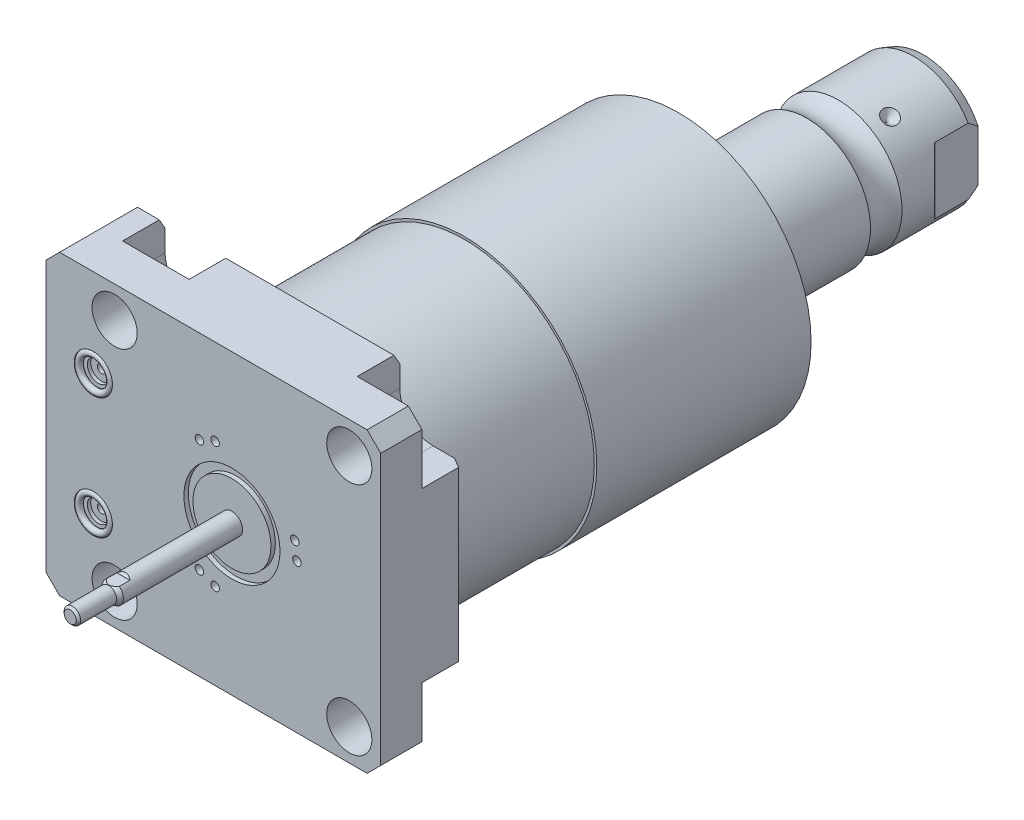
SolidWorks part; units mm, degrees
material "Alloy Steel"
ref_plane "Front Plane" through (0, 0, 0) normal (0, 0, 1) x (1, 0, 0)
ref_plane "Top Plane" through (0, 0, 0) normal (0, 1, 0) x (1, 0, 0)
ref_plane "Right Plane" through (0, 0, 0) normal (1, 0, 0) x (0, 0, -1)
sketch "Sketch1" plane through (0, 0, 0) normal (0, 0, 1) x (1, 0, 0)
  line L0 (-55.55, 44.45) -> (44.45, 44.45)
  line L1 (44.45, 44.45) -> (44.45, -44.45)
  line L2 (44.45, -44.45) -> (-55.55, -44.45)
  line L3 (-55.55, -44.45) -> (-55.55, 44.45)
  dimension "D1" = 100
  dimension "D2" = 88.9
  dimension "D3" = 44.45
  dimension "D4" = 44.45
extrude "Extrude1" add sketch "Sketch1" along normal blind 25.019
hole_wizard "Hole1" positions "Sketch22" profile "Sketch21" legacy end condition through all
sketch "Sketch22" plane through (0, 0, 0) normal (0, 0, -1) x (-1, 0, 0)
  line L0 (0, 0) -> (42.7441, 0) construction
  line L1 (0, 0.8532) -> (0, 27.5062) construction
  point P0 (-35.052, -35.052)
  point P9 (-35.052, 35.052)
  point P11 (35.052, 35.052)
  point P12 (35.052, -35.052)
  dimension "D1" = 35.052
  dimension "D2" = 35.052
sketch "Sketch21" plane through (35.052, -35.052, 0) normal (1, 0, 0) x (0, 1, 0)
  line L0 (0, 0) -> (0, 25.019)
  line L1 (0, 25.019) -> (6.7435, 25.019)
  line L2 (6.7435, 25.019) -> (6.7435, 0)
  line L3 (6.7435, 0) -> (0, 0)
  line L4 (0, 110) -> (0, -10) construction
  dimension "Diameter" = 13.487
  dimension "Depth" = 25.019
sketch "Sketch3" plane through (0, 0, 0) normal (0, 0, -1) x (-1, 0, 0)
  line L0 (-35.052, -25.1205) -> (-44.45, -25.1205)
  line L1 (-44.45, -44.45) -> (-44.45, -25.1205)
  line L2 (-44.45, 25.1205) -> (-44.45, 44.45)
  line L3 (-44.45, 25.1205) -> (-35.052, 25.1205)
  line L4 (-25.1205, 35.052) -> (-25.1205, 44.45)
  line L5 (-44.45, 44.45) -> (-25.1205, 44.45)
  line L6 (25.1205, 44.45) -> (25.1205, 35.052)
  line L7 (44.9835, 35.052) -> (44.9835, 44.45)
  line L8 (25.1205, 44.45) -> (44.9835, 44.45)
  line L9 (44.9835, -44.45) -> (25.1205, -44.45)
  line L10 (44.9835, -44.45) -> (44.9835, -35.052)
  line L11 (25.1205, -35.052) -> (25.1205, -44.45)
  line L12 (-25.1205, -44.45) -> (-44.45, -44.45)
  line L13 (-25.1205, -44.45) -> (-25.1205, -35.052)
  line L14 (-44.45, 44.45) -> (55.55, 44.45) construction
  line L15 (-44.45, -44.45) -> (-44.45, 44.45) construction
  line L16 (55.55, -44.45) -> (-44.45, -44.45) construction
  arc A0 (-25.1205, -35.052) -> (-35.052, -25.1205) centre (-35.052, -35.052) ccw
  arc A1 (-35.052, 25.1205) -> (-25.1205, 35.052) centre (-35.052, 35.052) ccw
  arc A2 (25.1205, 35.052) -> (44.9835, 35.052) centre (35.052, 35.052) ccw
  arc A3 (44.9835, -35.052) -> (25.1205, -35.052) centre (35.052, -35.052) ccw
  circle A8 centre (-35.052, 35.052) radius 6.7435 construction
  circle A9 centre (-35.052, -35.052) radius 6.7435 construction
  circle A10 centre (35.052, -35.052) radius 6.7435 construction
  circle A11 centre (35.052, 35.052) radius 6.7435 construction
  dimension "D1" = 9.9315
extrude "Cut-Extrude2" cut sketch "Sketch3" against normal blind 12.7
ref_plane "Plane16" through (0, 0, 12.014) normal (0, 0, 1) x (1, 0, 0)
sketch "Sketch23" plane through (0, 0, 12.014) normal (0, 0, 1) x (1, 0, 0)
  line L0 (-11.9397, -13.0048) -> (-61.0013, -13.0048) construction
  line L1 (-55.55, -23.749) -> (-55.296, -23.749)
  line L3 (-55.296, -23.749) -> (-55.296, -19.6596)
  line L4 (-55.296, -19.6596) -> (-54.5848, -18.9484)
  line L5 (-54.5848, -18.9484) -> (-41.1228, -18.9484)
  line L6 (-41.1228, -18.9484) -> (-41.1228, -13.0048)
  line L7 (-41.1228, -13.0048) -> (-55.55, -13.0048)
  line L8 (-55.55, -13.0048) -> (-55.55, -23.749)
  line L10 (-55.55, 44.45) -> (-55.55, -44.45) construction
  dimension "D1" = 21.4884
  dimension "D2" = 0.254
  dimension "D3" = 45
  dimension "D4" = 13.3096
  dimension "D5" = 11.8872
  dimension "D6" = 14.1732
  dimension "D7" = 13.0048
revolve "Cut-Revolve5" cut sketch "Sketch23" angle 360 about L0
mirror "Mirror1" about plane through (0, 0, 0) normal (0, 1, 0) of "Cut-Revolve5"
sketch "Sketch6" plane through (0, 0, 25.019) normal (0, 0, 1) x (1, 0, 0)
  line L0 (0, 0) -> (-71.0417, 0) construction
  circle A0 centre (-41.402, -18.11) radius 5.7023
  circle A1 centre (-41.402, 18.11) radius 5.7023
  dimension "D4" = 11.4046
  dimension "D1" = 18.11
  dimension "D2" = 36.22
  dimension "D3" = 41.402
extrude "Cut-Extrude3" cut sketch "Sketch6" against normal blind 1.4478
sketch "Sketch7" plane through (0, 0, 23.5712) normal (0, 0, 1) x (1, 0, 0)
  circle A0 centre (-41.402, 18.11) radius 3.2512
  circle A1 centre (-41.402, -18.11) radius 3.2512
  circle A2 centre (-41.402, 18.11) radius 5.7023 construction
  circle A3 centre (-41.402, -18.11) radius 5.7023 construction
  dimension "D1" = 6.5024
extrude "Cut-Extrude4" cut sketch "Sketch7" against normal blind 1.016
sketch "Sketch8" plane through (0, 0, 22.5552) normal (0, 0, 1) x (1, 0, 0)
  circle A0 centre (-41.402, 18.11) radius 1.2446
  circle A1 centre (-41.402, -18.11) radius 1.2446
  circle A2 centre (-41.402, 18.11) radius 5.7023 construction
  circle A3 centre (-41.402, -18.11) radius 5.7023 construction
  dimension "D1" = 2.4892
extrude "Cut-Extrude5" cut sketch "Sketch8" against normal blind 11.9888
ref_plane "Plane17" through (0, 18.11, 0) normal (0, 1, 0) x (-1, 0, 0)
sketch "Sketch9" plane through (-41.656, 18.11, 23.5712) normal (0, 1, 0) x (1, 0, 0)
  line L0 (0.254, -1.9469) -> (0.254, 0.0927) construction
  line L3 (-5.4483, 0) -> (5.9563, 0) construction
  line L4 (0.254, 13.0048) -> (0.254, 1.016) construction
  circle A0 centre (5.0292, -0.9271) radius 0.9271
  dimension "D1" = 1.8542
  dimension "D2" = 9.5504
revolve "Revolve1" add sketch "Sketch9" angle 360 about L0
mirror "Mirror2" about plane through (0, 0, 0) normal (0, 1, 0) of bodies 116
chamfer "Chamfer1" distance 4.064 angle 45 4 edges at (44.45, -44.45, 18.8595) (44.45, 44.45, 18.8595) (-55.55, 44.45, 12.5095) (-55.55, -44.45, 12.5095)
chamfer "Chamfer2" distance 3.0226 angle 30 5 edges at (-48.2347, -44.45, 0) (0, -44.45, 0) (44.45, 0, 0) (-48.2347, 44.45, 0) (0, 44.45, 0)
sketch "Sketch24" plane through (0, 0, 0) normal (1, 0, 0) x (0, 0, -1)
  line L0 (0, 0) -> (113.9127, 0) construction
  line L1 (0, 0) -> (0, 38.786)
  line L2 (0, 38.786) -> (44.45, 38.786)
  line L3 (44.45, 38.786) -> (44.45, 39.5225)
  line L4 (44.45, 39.5225) -> (108.4839, 39.5225)
  line L5 (108.4839, 39.5225) -> (112.268, 25.4)
  line L6 (112.268, 25.4) -> (112.268, 0)
  line L7 (112.268, 0) -> (0, 0)
  dimension "D1" = 77.572
  dimension "D2" = 44.45
  dimension "D3" = 79.045
  dimension "D4" = 50.8
  dimension "D5" = 15
  dimension "D6" = 112.268
revolve "Revolve4" add sketch "Sketch24" angle 360 about L0
sketch "Sketch17" plane through (0, 0, 0) normal (1, 0, 0) x (0, 0, -1)
  line L0 (112.268, 0) -> (112.268, -19.05)
  line L1 (112.268, -19.05) -> (146.7029, -19.05)
  line L2 (156.1171, -19.05) -> (178.664, -19.05)
  line L3 (181.585, -17.9868) -> (181.585, 0)
  line L4 (181.585, 0) -> (112.268, 0)
  line L5 (130.8989, 0) -> (0.816, 0) construction
  line L6 (112.268, -25.4) -> (112.268, 25.4) construction
  line L7 (-25.019, -40.386) -> (-25.019, 40.386) construction
  line L8 (181.585, -17.9868) -> (178.664, -19.05)
  arc A0 (156.1171, -19.05) -> (146.7029, -19.05) centre (151.41, -25.4254) ccw
  dimension "D2" = 20
  dimension "D4" = 7.9248
  dimension "D5" = 35.0012
  dimension "D1" = 206.604
  dimension "D3" = 38.1
  dimension "D6" = 30.175
  dimension "D7" = 2.921
revolve "Revolve3" add sketch "Sketch17" angle 360 about L5
sketch "Sketch28" plane through (0, 0, 0) normal (0, 1, 0) x (1, 0, 0)
  line L0 (-34.3062, 162.078) -> (35.4095, 162.078) construction
  line L1 (-19.05, 164.491) -> (-16.637, 162.078)
  line L2 (-19.05, 178.664) -> (-19.05, 156.1171) construction
  line L3 (-16.637, 162.078) -> (-19.05, 162.078)
  line L4 (-19.05, 162.078) -> (-19.05, 164.491)
  arc A0 (-19.05, 146.7029) -> (-19.05, 156.1171) centre (-25.4254, 151.41) ccw construction
  dimension "D3" = 10.668
  dimension "D1" = 45
  dimension "D2" = 4.826
revolve "Cut-Revolve6" cut sketch "Sketch28" angle 360 about L0
pattern_circular "CirPattern1" count 3 over 360 about axis through (0, 0, -130.8989) along (0, 0, -1) of "Cut-Revolve6"
hole_wizard "Hole2" positions "Sketch33" profile "Sketch32" legacy
sketch "Sketch33" plane through (0, 0, -181.585) normal (0, 0, -1) x (-1, 0, 0)
  circle A0 centre (0, 0) radius 19.05 construction
  point P0 (0, 0)
sketch "Sketch32" plane through (0, 0, -181.585) normal (1, 0, 0) x (0, 1, 0)
  line L0 (0, 0) -> (0, 29.5665)
  line L1 (0, 29.5665) -> (6.9342, 25.4)
  line L2 (6.9342, 25.4) -> (6.9342, 0)
  line L4 (6.9342, 0) -> (0, 0)
  line L6 (0, 29.5665) -> (-6.9342, 25.4) construction
  line L7 (0, -4.2442) -> (0, 117.3081) construction
  dimension "Diameter" = 13.8684
  dimension "Depth" = 25.4
  dimension "Drill Angle" = 118
sketch "Sketch34" plane through (0, 0, 0) normal (0, 1, 0) x (0, 0, -1)
  line L0 (0, 0) -> (211.3651, 0) construction
  line L1 (165.8009, 19.05) -> (168.3462, 16.5047)
  line L3 (168.885, 16.2815) -> (181.585, 16.2815)
  line L4 (181.585, -17.9868) -> (181.585, 17.9868) construction
  line L5 (181.585, 16.2815) -> (181.585, 19.05)
  line L6 (181.585, 19.05) -> (165.8009, 19.05)
  line L7 (181.585, -19.05) -> (165.8009, -19.05)
  line L8 (181.585, -16.2815) -> (181.585, -19.05)
  line L9 (168.885, -16.2815) -> (181.585, -16.2815)
  line L10 (165.8009, -19.05) -> (168.3462, -16.5047)
  line L11 (178.664, 19.05) -> (164.491, 19.05) construction
  arc A0 (168.885, 16.2815) -> (168.3462, 16.5047) centre (168.885, 17.0435) cw
  arc A1 (168.885, -16.2815) -> (168.3462, -16.5047) centre (168.885, -17.0435) ccw
  dimension "D2" = 0.762
  dimension "D1" = 45
  dimension "D3" = 12.7
  dimension "D4" = 32.563
extrude "Cut-Extrude8" cut sketch "Sketch34" against normal through all and the other way through all
sketch "Sketch35" plane through (0, 0, 0) normal (1, 0, 0) x (0, 0, -1)
  line L0 (-1000, 0) -> (49000, 0) construction
  line L1 (-25.019, 0) -> (-25.019, -3.175)
  line L2 (-25.019, -40.386) -> (-25.019, 40.386) construction
  line L3 (-25.019, -3.175) -> (-60.6231, -3.175)
  line L4 (-60.6231, -3.175) -> (-61.899, -2.4384)
  line L5 (-61.899, -2.4384) -> (-72.694, -2.4384)
  line L6 (-72.694, -2.4384) -> (-73.329, -1.8034)
  line L7 (-73.329, -1.8034) -> (-73.329, 0)
  line L8 (-73.329, 0) -> (-25.019, 0)
  line L9 (181.585, -17.9868) -> (181.585, -7.6446) construction
  dimension "D1" = 45
  dimension "D2" = 0.635
  dimension "D3" = 30
  dimension "D4" = 4.8768
  dimension "D5" = 6.35
  dimension "D6" = 11.43
  dimension "D7" = 254.914
revolve "Revolve5" add sketch "Sketch35" angle 360 about L0
sketch "Sketch36" plane through (0, 0, 0) normal (1, 0, 0) x (0, 0, -1)
  line L0 (-1000, 0) -> (49000, 0) construction
  line L1 (-56.7809, -3.175) -> (-57.454, -2.5019)
  line L2 (-60.6231, -3.175) -> (-25.019, -3.175) construction
  line L3 (-57.454, -2.5019) -> (-73.329, -2.5019)
  line L4 (-73.329, 1.8034) -> (-73.329, -1.8034) construction
  line L5 (-56.7809, -3.175) -> (-73.329, -3.175)
  line L6 (-73.329, -3.175) -> (-73.329, -2.5019)
  line L7 (-56.7809, 3.175) -> (-57.454, 2.5019)
  line L8 (-57.454, 2.5019) -> (-73.329, 2.5019)
  line L9 (-56.7809, 3.175) -> (-73.329, 3.175)
  line L10 (-73.329, 3.175) -> (-73.329, 2.5019)
  dimension "D1" = 45
  dimension "D2" = 5.0038
  dimension "D3" = 15.875
extrude "Cut-Extrude9" cut sketch "Sketch36" against normal mid plane 7.62
sketch "Sketch37" plane through (0, 0, 0) normal (1, 0, 0) x (0, 0, -1)
  line L0 (-1000, 0) -> (49000, 0) construction
  line L1 (-25.019, -40.386) -> (-25.019, 40.386) construction
  line L2 (-25.019, -11.6459) -> (-23.6982, -11.6459)
  line L3 (-25.019, -11.6459) -> (-25.019, -14.351)
  line L4 (-25.019, -14.351) -> (-23.6982, -14.351)
  line L5 (-23.6982, -11.6459) -> (-23.6982, -14.351)
  dimension "D1" = 23.2918
  dimension "D2" = 28.7021
  dimension "D3" = 1.3208
revolve "Cut-Revolve7" cut sketch "Sketch37" angle 360 about L0
sketch "Sketch38" plane through (0, 0, 25.019) normal (0, 0, 1) x (1, 0, 0)
  line L0 (-1000, 0) -> (49000, 0) construction
  line L1 (0, 0) -> (48296.2913, 12940.9523) construction
  line L2 (0, 0) -> (25000, 43301.2702) construction
  circle A0 centre (0, 0) radius 19.431 construction
  circle A1 centre (19.431, 0) radius 1.27
  circle A2 centre (18.7689, 5.0291) radius 1.27
  circle A3 centre (-5.0291, 18.7689) radius 1.27
  circle A4 centre (-9.7155, 16.8278) radius 1.27
  circle A5 centre (-9.7155, -16.8278) radius 1.27
  circle A6 centre (-5.0291, -18.7689) radius 1.27
  dimension "D3" = 38.8621
  dimension "D4" = 2.54
  dimension "D5" = 2.54
  dimension "D1" = 15
  dimension "D2" = 60
extrude "Cut-Extrude10" cut sketch "Sketch38" against normal blind 7.62
